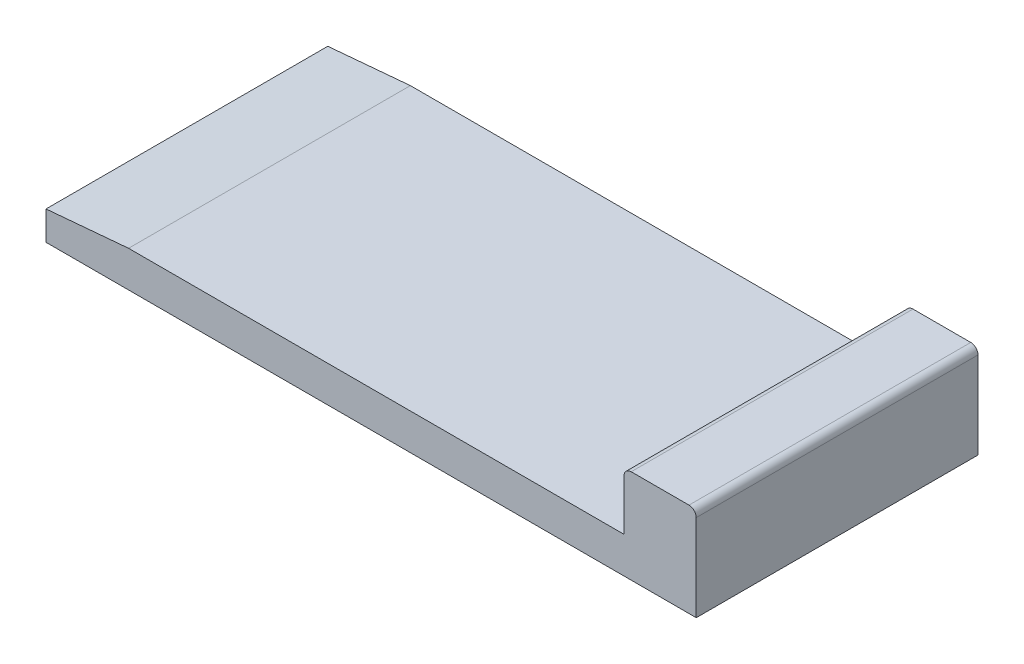
SolidWorks part; units mm, degrees
ref_plane "Front Plane" through (0, 0, 0) normal (0, 0, 1) x (1, 0, 0)
ref_plane "Top Plane" through (0, 0, 0) normal (0, 1, 0) x (1, 0, 0)
ref_plane "Right Plane" through (0, 0, 0) normal (1, 0, 0) x (0, 0, -1)
sketch "Sketch1" plane through (0, 0, 0) normal (0, 1, 0) x (1, 0, 0)
  line L1 (-21.2148, 8.6125) -> (23.7852, 8.6125)
  line L2 (-21.2148, 8.6125) -> (-21.2148, -10.8875)
  line L3 (-21.2148, -10.8875) -> (23.7852, -10.8875)
  line L4 (23.7852, 8.6125) -> (23.7852, -10.8875)
  dimension "D1" = 45
  dimension "D2" = 19.5
extrude "Boss-Extrude1" add sketch "Sketch1" along normal blind 2.5
sketch "Sketch2" plane through (0, 2.5, 0) normal (0, 1, 0) x (1, 0, 0)
  line L0 (-21.2148, -10.8875) -> (23.7852, -10.8875) construction
  line L1 (23.7852, 8.6125) -> (18.7852, 8.6125)
  line L2 (23.7852, 8.6125) -> (23.7852, -10.8875)
  line L3 (23.7852, -10.8875) -> (18.7852, -10.8875)
  line L4 (18.7852, 8.6125) -> (18.7852, -10.8875)
  dimension "D1" = 5
extrude "Boss-Extrude2" add sketch "Sketch2" along normal blind 4
fillet "Fillet1" radius 0.5 2 edges at (18.7852, 6.5, 1.1375) (23.7852, 6.5, 1.1375)
chamfer "Chamfer1" distance 0.5 angle 85 1 edges at (-21.2148, 2.5, 1.1375)
